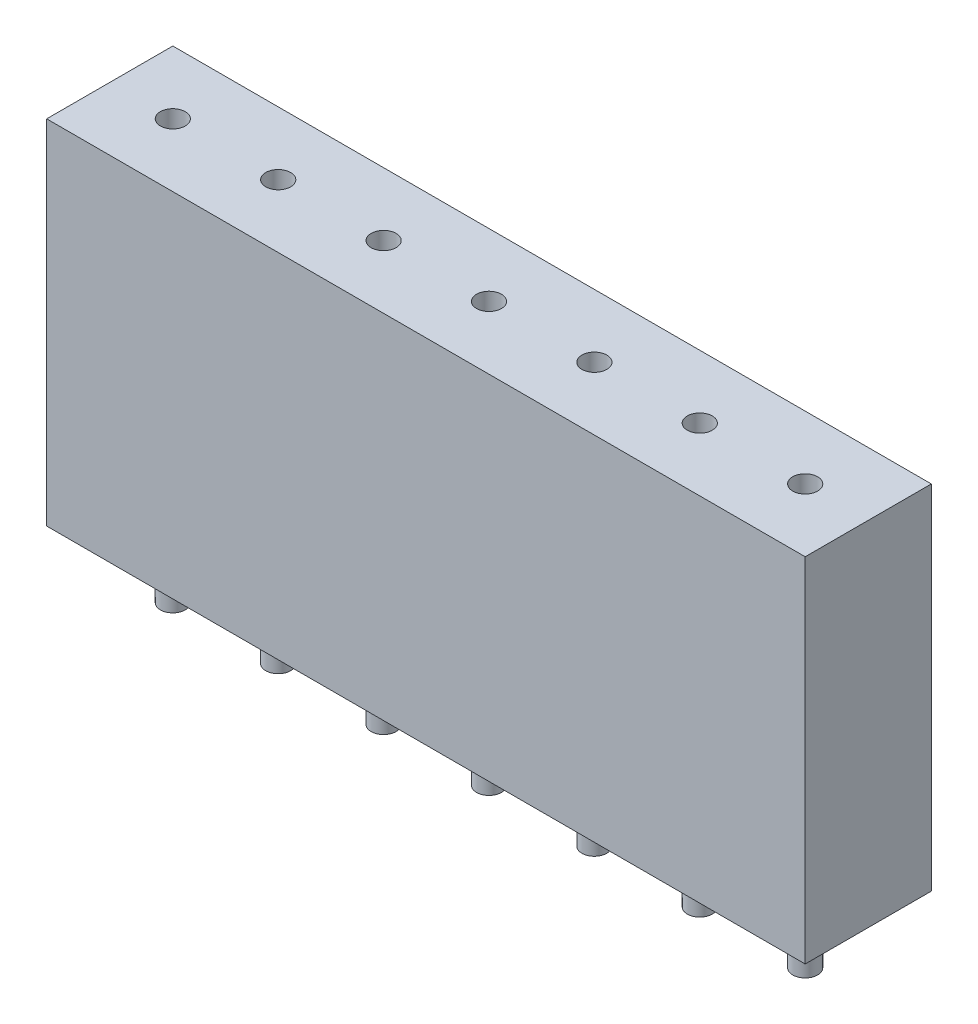
SolidWorks part; units mm, degrees
ref_plane "Спереди" through (0, 0, 0) normal (0, 0, 1) x (1, 0, 0)
ref_plane "Сверху" through (0, 0, 0) normal (0, 1, 0) x (1, 0, 0)
ref_plane "Справа" through (0, 0, 0) normal (1, 0, 0) x (0, 0, -1)
sketch "Эскиз1" plane through (0, 0, 0) normal (0, 1, 0) x (1, 0, 0)
  line L1 (-9.14, 1.52) -> (9.14, 1.52)
  line L2 (-9.14, 1.52) -> (-9.14, -1.52)
  line L3 (-9.14, -1.52) -> (9.14, -1.52)
  line L4 (9.14, 1.52) -> (9.14, -1.52)
  line L5 (-9.14, 1.52) -> (9.14, -1.52) construction
  line L6 (-9.14, -1.52) -> (9.14, 1.52) construction
  point P0 (0, 0)
extrude "Бобышка-Вытянуть1" add sketch "Эскиз1" along normal blind 8.5
sketch "Эскиз2" plane through (0, 8.5, 0) normal (0, 1, 0) x (1, 0, 0)
  circle A0 centre (-7.62, 0) radius 0.3
  circle A1 centre (-5.08, 0) radius 0.3
  circle A2 centre (-2.54, 0) radius 0.3
  circle A3 centre (0, 0) radius 0.3
  circle A4 centre (2.54, 0) radius 0.3
  circle A5 centre (5.08, 0) radius 0.3
  circle A6 centre (7.62, 0) radius 0.3
  dimension "D1" = 7
extrude "Вырез-Вытянуть1" cut sketch "Эскиз2" against normal blind 8.5
sketch "Эскиз3" plane through (0, 0, 0) normal (0, -1, 0) x (1, 0, 0)
  circle A0 centre (-7.62, 0) radius 0.3
  circle A1 centre (-5.08, 0) radius 0.3
  circle A2 centre (-2.54, 0) radius 0.3
  circle A3 centre (0, 0) radius 0.3
  circle A4 centre (2.54, 0) radius 0.3
  circle A5 centre (5.08, 0) radius 0.3
  circle A6 centre (7.62, 0) radius 0.3
  dimension "D1" = 7
extrude "Бобышка-Вытянуть2" add sketch "Эскиз3" along normal blind 1.6 separate body
